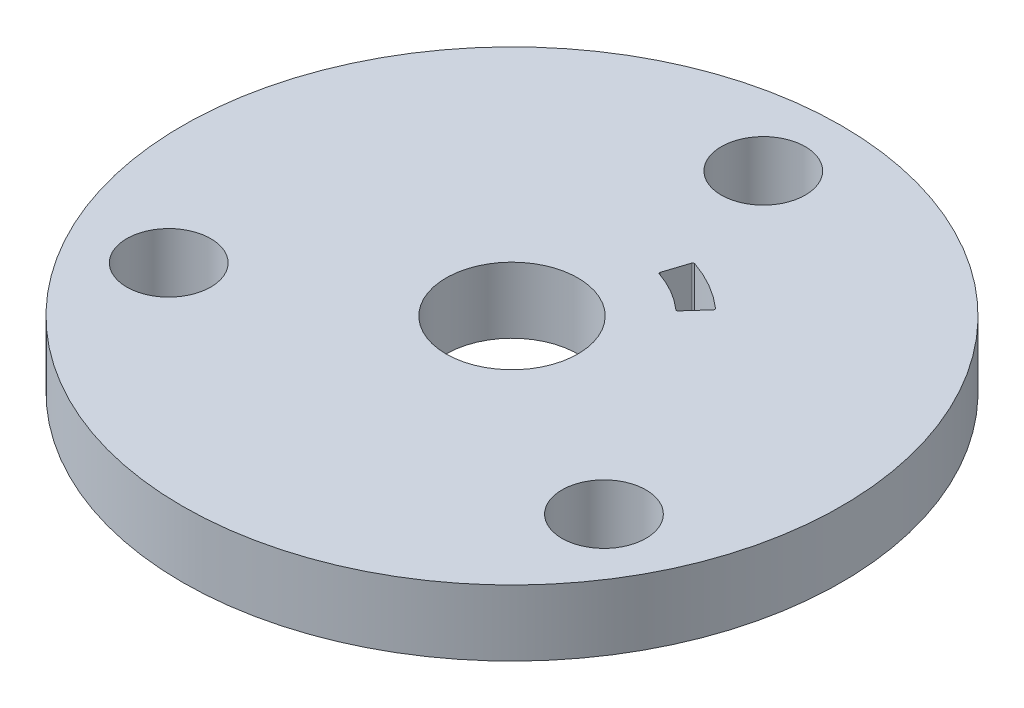
SolidWorks part; units mm, degrees
ref_plane "Front Plane" through (0, 0, 0) normal (0, 0, 1) x (1, 0, 0)
ref_plane "Top Plane" through (0, 0, 0) normal (0, 1, 0) x (1, 0, 0)
ref_plane "Right Plane" through (0, 0, 0) normal (1, 0, 0) x (0, 0, -1)
sketch "Sketch1" plane through (0, 0, 0) normal (0, 1, 0) x (1, 0, 0)
  circle A0 centre (0, 0) radius 20
  circle A2 centre (0, 0) radius 4
  dimension "D1" = 40
  dimension "D2" = 8
extrude "Boss-Extrude1" add sketch "Sketch1" along normal blind 4
sketch "Sketch2" plane through (0, 4, 0) normal (0, 1, 0) x (1, 0, 0)
  circle A0 centre (0, 0) radius 15.25 construction
  circle A1 centre (0, 15.25) radius 2.55
  dimension "D1" = 5.1
  dimension "D2" = 30.5
extrude "Cut-Extrude2" cut sketch "Sketch2" against normal through all
pattern_circular "CirPattern1" count 3 over 360 about axis through (0, 0, 0) along (0, 1, 0) of "Cut-Extrude2"
sketch "Sketch3" plane through (0, 4, 0) normal (0, 1, 0) x (1, 0, 0)
  line L0 (0, 0) -> (2.7039, 8.3217) construction
  line L1 (0, 0) -> (5.8549, 6.5025) construction
  line L2 (4.375, 7.5777) -> (0, 0) construction
  line L3 (2.7039, 8.3217) -> (2.1786, 6.7049)
  line L4 (5.8549, 6.5025) -> (4.7174, 5.2392)
  line L5 (0, 0) -> (8.75, 0) construction
  circle A0 centre (0, 0) radius 7.05 construction
  circle A1 centre (0, 0) radius 8.75 construction
  arc A2 (2.7039, 8.3217) -> (5.8549, 6.5025) centre (0, 0) cw
  arc A3 (2.1786, 6.7049) -> (4.7174, 5.2392) centre (0, 0) cw
  dimension "D1" = 17.5
  dimension "D2" = 14.1
  dimension "D3" = 24
  dimension "D4" = 12
  dimension "D5" = 60
extrude "Cut-Extrude3" cut sketch "Sketch3" against normal through all
fillet "Fillet1" radius 0.1 4 edges at (2.1786, 2, -6.7049) (4.7174, 2, -5.2392) (5.8549, 2, -6.5025) (2.7039, 2, -8.3217)
